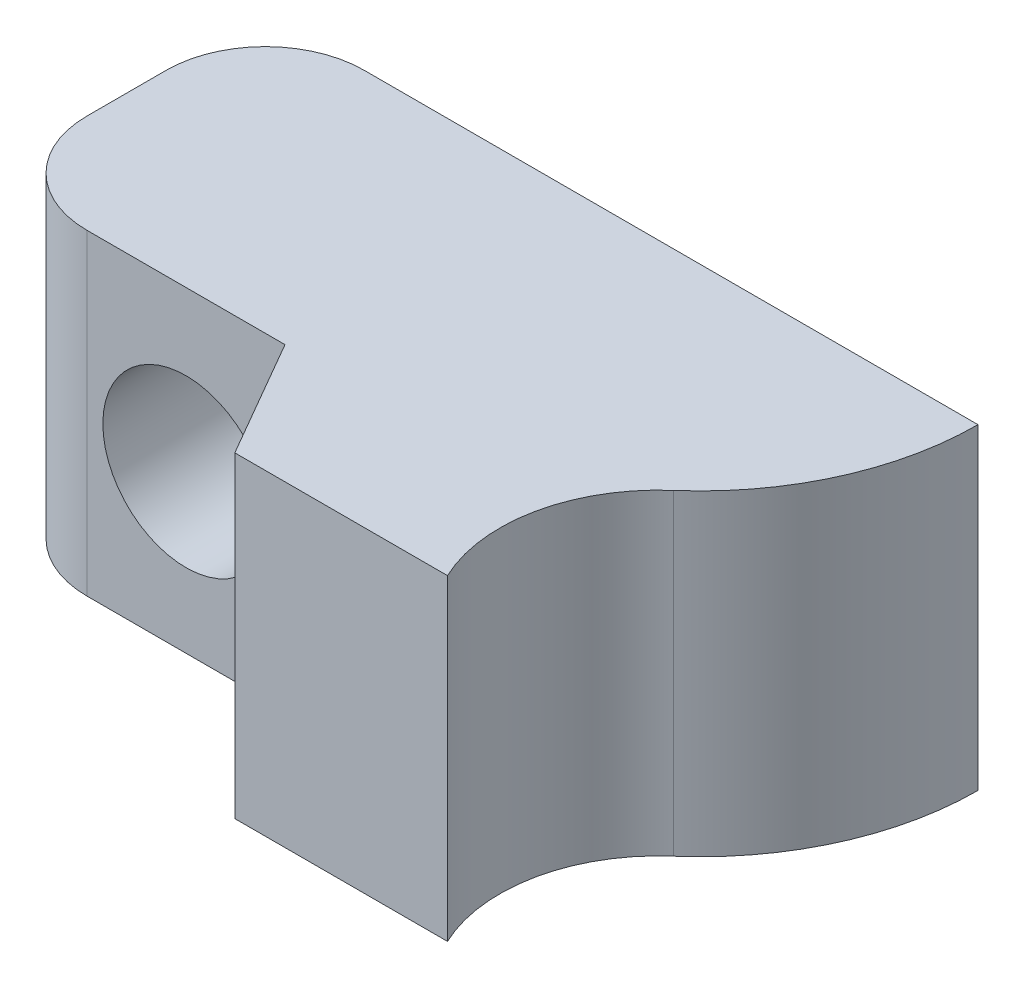
SolidWorks part; units mm, degrees
ref_plane "Front Plane" through (0, 0, 0) normal (0, 0, 1) x (1, 0, 0)
ref_plane "Top Plane" through (0, 0, 0) normal (0, 1, 0) x (1, 0, 0)
ref_plane "Right Plane" through (0, 0, 0) normal (1, 0, 0) x (0, 0, -1)
sketch "Sketch1" plane through (0, 0, 0) normal (0, 0, 1) x (1, 0, 0)
  line L1 (-5, 4.0277) -> (13, 4.0277)
  line L2 (-5, 4.0277) -> (-5, -3.9723)
  line L3 (-5, -3.9723) -> (13, -3.9723)
  line L4 (13, 4.0277) -> (13, -3.9723)
  circle A0 centre (0, 0) radius 1.6
  point P7 (0, 0)
  dimension "D1" = 3.2
  dimension "D2" = 13
  dimension "D3" = 8
  dimension "D4" = 5
extrude "Boss-Extrude1" add sketch "Sketch1" along normal blind 10
sketch "Sketch2" plane through (0, -3.9723, 0) normal (0, -1, 0) x (1, 0, 0)
  line L0 (13.2216, 12.2975) -> (13, 0)
  arc A2 (13, 0) -> (10.5955, 5.2802) centre (6, 0) ccw
  arc A3 (13.2216, 12.2975) -> (10.5955, 5.2802) centre (13.2216, 8.2975) ccw
extrude "Cut-Extrude1" cut sketch "Sketch2" against normal through all both and the other way through all
sketch "Sketch3" plane through (0, 4.0277, 0) normal (0, 1, 0) x (1, 0, 0)
  line L0 (-1.6, -10) -> (1.6, -10) construction
  line L1 (-1.6, -10) -> (1.6, -10) construction
  line L2 (1.6, -10) -> (2.5, -10) construction
  line L3 (9.602, -10) -> (-5, -10) construction
  line L8 (-5, -7) -> (2.5, -7)
  line L10 (2.5, -7) -> (4.2321, -10)
  line L11 (4.2321, -10) -> (-5, -10)
  line L12 (-5, -10) -> (-5, -7)
  point P2 (0, -10)
  dimension "D1" = 60
  dimension "D2" = 2.5
  dimension "D3" = 3
extrude "Cut-Extrude3" cut sketch "Sketch3" against normal through all both and the other way through all
fillet "Fillet1" radius 2.5 2 edges at (-5, 0.0277, 7) (-5, 0.0277, 0)
sketch "Sketch4" plane through (0, 0, 7) normal (0, 0, 1) x (1, 0, 0)
  circle A0 centre (0, 0) radius 2.1
  dimension "D1" = 4.2
extrude "Cut-Extrude4" cut sketch "Sketch4" against normal blind 5 and the other way through all
